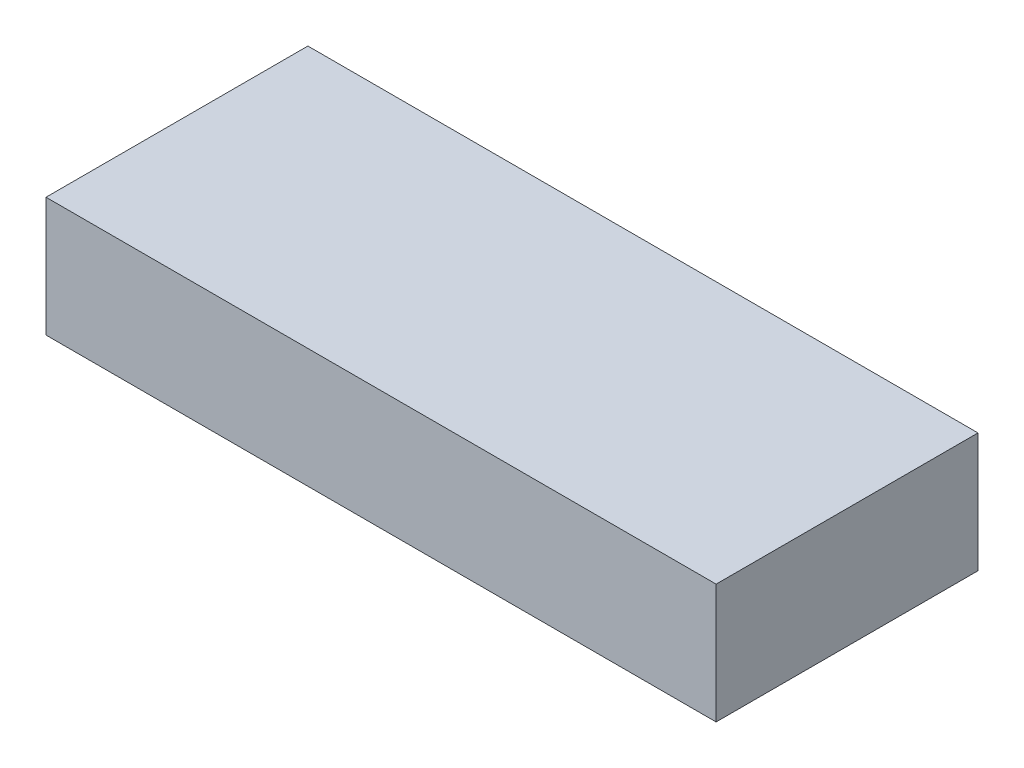
SolidWorks part; units mm, degrees
ref_plane "正面" through (0, 0, 0) normal (0, 0, 1) x (1, 0, 0)
ref_plane "平面" through (0, 0, 0) normal (0, 1, 0) x (1, 0, 0)
ref_plane "右側面" through (0, 0, 0) normal (1, 0, 0) x (0, 0, -1)
sketch "ｽｹｯﾁ1" plane through (0, 0, 0) normal (0, 1, 0) x (1, 0, 0)
  line L1 (0, 0) -> (87, 0)
  line L2 (0, 0) -> (0, 34)
  line L3 (0, 34) -> (87, 34)
  line L4 (87, 0) -> (87, 34)
extrude "ﾎﾞｽ - 押し出し1" add sketch "ｽｹｯﾁ1" along normal blind 15.5
